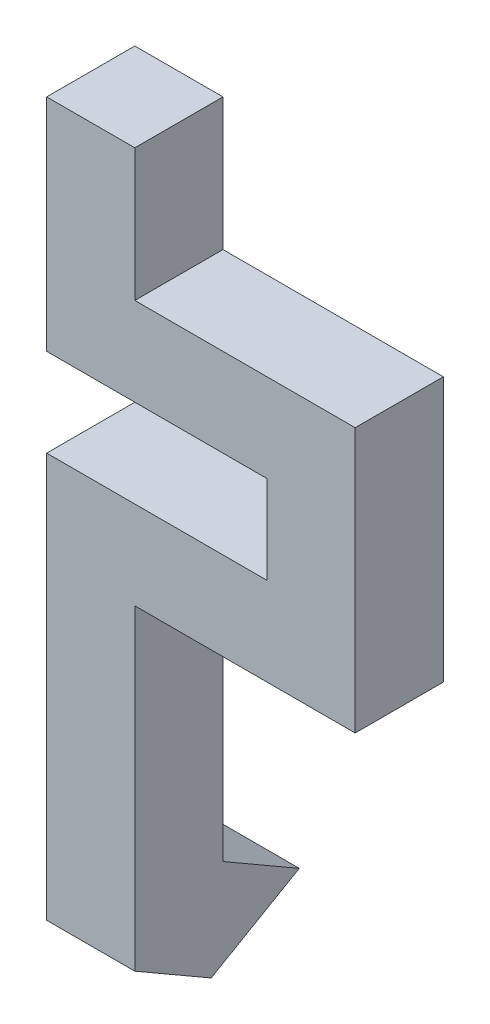
SolidWorks part; units mm, degrees
ref_plane "Front" through (0, 0, 0) normal (0, 0, 1) x (1, 0, 0)
ref_plane "Top" through (0, 0, 0) normal (0, 1, 0) x (1, 0, 0)
ref_plane "Right" through (0, 0, 0) normal (1, 0, 0) x (0, 0, -1)
sketch "草图1" plane through (0, 0, 0) normal (0, 0, 1) x (1, 0, 0)
  line L1 (0, 0) -> (2, 0)
  line L2 (0, 0) -> (0, -5)
  line L3 (0, -5) -> (2, -5)
  line L4 (2, 0) -> (2, -5)
  line L5 (2, -5) -> (7, -5)
  line L6 (2, -5) -> (2, -3)
  line L7 (2, -3) -> (7, -3)
  line L8 (7, -5) -> (7, -3)
  line L9 (7, -5) -> (5, -5)
  line L10 (7, -5) -> (7, -9)
  line L11 (7, -9) -> (5, -9)
  line L12 (5, -5) -> (5, -9)
  line L13 (5, -9) -> (0, -9)
  line L14 (5, -9) -> (5, -7)
  line L15 (5, -7) -> (0, -7)
  line L16 (0, -9) -> (0, -7)
  line L17 (0, -9) -> (2, -9)
  line L18 (0, -9) -> (0, -16.18)
  line L19 (0, -16.18) -> (2, -16.18)
  line L20 (2, -9) -> (2, -16.18)
  dimension "D1" = 2
  dimension "D2" = 5
  dimension "D3" = 2
  dimension "D4" = 2
  dimension "D5" = 2
  dimension "D6" = 4
  dimension "D7" = 5
  dimension "D8" = 5
  dimension "D9" = 7.18
extrude "凸台-拉伸1" add sketch "草图1" along normal blind 2 contours L20 L13 L18 L19 | L16 L13 L12 L15 | L5 L12 L11 L10 | L4 L1 L2 L3 | L5 L8 L7 L4
sketch "草图2" plane through (0, 0, 0) normal (-1, 0, 0) x (0, 0, 1)
  line L0 (2, -16.18) -> (0.2679, -17.18)
  line L1 (0, -15.0253) -> (-1.7321, -16.0253)
  line L2 (2, -7) -> (2, -16.18) construction
  line L3 (2, -16.18) -> (0, -15.0253)
  line L4 (-1.7321, -16.0253) -> (0.2679, -17.18)
  dimension "D1" = 120
  dimension "D2" = 60
  dimension "D4" = 2
  dimension "D5" = 2
  dimension "D6" = 2
extrude "凸台-拉伸2" add sketch "草图2" against normal blind 2
